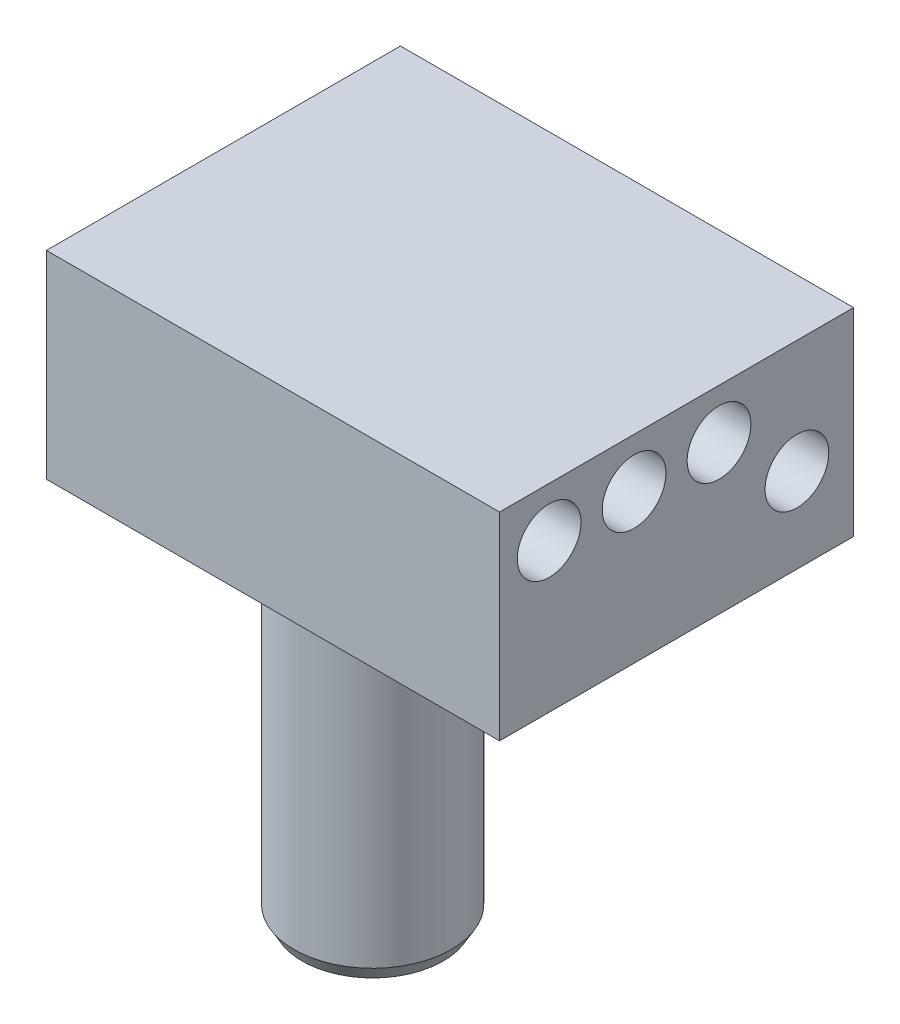
SolidWorks part; units mm, degrees
ref_plane "Front Plane" through (0, 0, 0) normal (0, 0, 1) x (1, 0, 0)
ref_plane "Top Plane" through (0, 0, 0) normal (0, 1, 0) x (1, 0, 0)
ref_plane "Right Plane" through (0, 0, 0) normal (1, 0, 0) x (0, 0, -1)
sketch "Sketch1" plane through (0, 0, 0) normal (1, 0, 0) x (0, 0, -1)
  line L1 (-12.5, -7) -> (12.5, -7)
  line L2 (-12.5, -7) -> (-12.5, 7)
  line L3 (-12.5, 7) -> (12.5, 7)
  line L4 (12.5, -7) -> (12.5, 7)
  line L5 (-12.5, -7) -> (12.5, 7) construction
  line L6 (-12.5, 7) -> (12.5, -7) construction
  circle A0 centre (8.5, -1) radius 2.25
  circle A1 centre (3, 3.5) radius 2.25
  circle A2 centre (-3, 3.5) radius 2.25
  circle A3 centre (-9, 3.5) radius 2.25
  point P0 (0, 0)
  dimension "D7" = 4.5
  dimension "D8" = 4.5
  dimension "D9" = 4.5
  dimension "D10" = 4.5
  dimension "D1" = 25
  dimension "D2" = 14
  dimension "D3" = 3.5
  dimension "D4" = 6
  dimension "D5" = 6
  dimension "D6" = 5.5
  dimension "D11" = 3.5
  dimension "D12" = 4.5
extrude "Boss-Extrude1" add sketch "Sketch1" along normal blind 20
sketch "Sketch2" plane through (0, 0, 0) normal (-1, 0, 0) x (0, 0, 1)
  line L1 (-12.5, -7) -> (12.5, -7)
  line L2 (-12.5, -7) -> (-12.5, 7)
  line L3 (-12.5, 7) -> (12.5, 7)
  line L4 (12.5, -7) -> (12.5, 7)
  line L5 (-12.5, -7) -> (12.5, 7) construction
  line L6 (-12.5, 7) -> (12.5, -7) construction
  point P0 (0, 0)
extrude "Boss-Extrude2" add sketch "Sketch2" along normal blind 12
sketch "Sketch3" plane through (0, -7, 0) normal (0, -1, 0) x (1, 0, 0)
  line L0 (-12, 0) -> (20, 0) construction
  line L1 (-12, -12.5) -> (-12, 12.5) construction
  line L2 (20, 12.5) -> (20, -12.5) construction
  circle A0 centre (-1, 0) radius 11
  dimension "D1" = 22
extrude "Boss-Extrude3" add sketch "Sketch3" along normal blind 1.5
sketch "Sketch4" plane through (0, -8.5, 0) normal (0, -1, 0) x (1, 0, 0)
  circle A0 centre (-1, 0) radius 10
  circle A1 centre (-1, 0.4618) radius 6.25
  dimension "D1" = 12.5
  dimension "D2" = 20
extrude "Cut-Extrude1" cut sketch "Sketch4" against normal blind 1.25
sketch "Sketch5" plane through (0, -8.5, 0) normal (0, -1, 0) x (1, 0, 0)
  circle A0 centre (-1, 0.4618) radius 5.5562
  dimension "D1" = 11.1125
extrude "Boss-Extrude4" add sketch "Sketch5" along normal blind 26
chamfer "Chamfer1" distance 1 angle 30 1 edges at (-1, -34.5, -5.0945)
